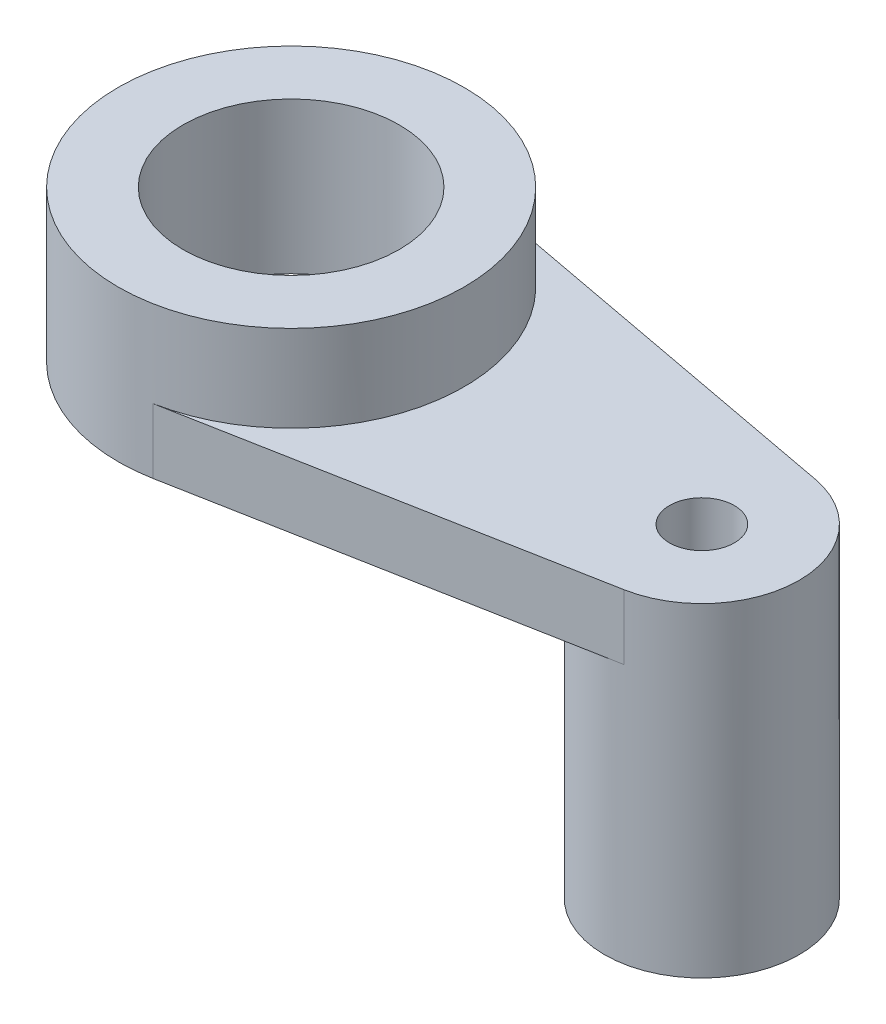
SolidWorks part; units mm, degrees
material "Galvanized Steel"
ref_plane "Front Plane" through (0, 0, 0) normal (0, 0, 1) x (1, 0, 0)
ref_plane "Top Plane" through (0, 0, 0) normal (0, 1, 0) x (1, 0, 0)
ref_plane "Right Plane" through (0, 0, 0) normal (1, 0, 0) x (0, 0, -1)
sketch "Sketch3" plane through (0, 0, 0) normal (0, 1, 0) x (1, 0, 0)
  line L0 (2.9474, 15.7262) -> (39.6579, 8.846)
  line L1 (2.9474, -15.7262) -> (39.6579, -8.846)
  circle A0 centre (0, 0) radius 16
  circle A1 centre (38, 0) radius 9
extrude "Boss-Extrude1" add sketch "Sketch3" along normal blind 6 contours A0 | A1 L0 A0 L1 | A1
sketch "Sketch4" plane through (0, 6, 0) normal (0, 1, 0) x (1, 0, 0)
  circle A0 centre (38, 0) radius 9
extrude "Boss-Extrude2" add sketch "Sketch4" against normal blind 30
sketch "Sketch5" plane through (0, 6, 0) normal (0, 1, 0) x (1, 0, 0)
  circle A0 centre (0, 0) radius 16
extrude "Boss-Extrude3" add sketch "Sketch5" along normal blind 8 contours A0
sketch "Sketch6" plane through (0, 14, 0) normal (0, 1, 0) x (1, 0, 0)
  circle A0 centre (0, 0) radius 10
extrude "Cut-Extrude1" cut sketch "Sketch6" against normal through all
sketch "Sketch7" plane through (0, 6, 0) normal (0, 1, 0) x (1, 0, 0)
  circle A0 centre (38, 0) radius 3
extrude "Cut-Extrude2" cut sketch "Sketch7" against normal through all
